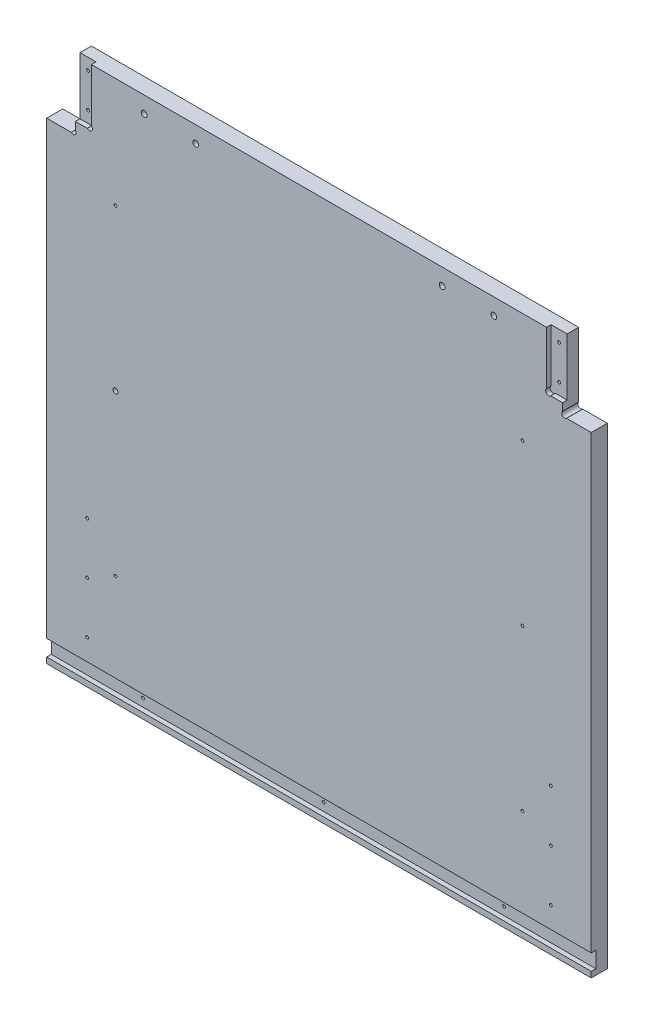
SolidWorks part; units mm, degrees
material "Pine"
ref_plane "Front Plane" through (0, 0, 0) normal (0, 0, 1) x (1, 0, 0)
ref_plane "Top Plane" through (0, 0, 0) normal (0, 1, 0) x (1, 0, 0)
ref_plane "Right Plane" through (0, 0, 0) normal (1, 0, 0) x (0, 0, -1)
sketch "Sketch1" plane through (0, 0, 0) normal (0, 0, 1) x (1, 0, 0)
  line L0 (8932.6508, -5243.5125) -> (10226.1458, -5243.5125)
  line L1 (9086.3208, -4722.0918) -> (10222.9708, -4853.7812)
  line L2 (8914.8708, -6342.0625) -> (10197.5708, -6342.0625)
  line L3 (8914.8708, -5808.6625) -> (10197.5708, -5808.6625)
  line L4 (8919.6333, -5253.0375) -> (10218.2083, -5253.0375)
  line L5 (9134.2633, -4656.1375) -> (9134.2633, -4638.3575)
  line L6 (9091.0833, -4638.3575) -> (9134.2633, -4638.3575)
  line L7 (9091.0833, -4567.2375) -> (9091.0833, -4638.3575)
  line L8 (9134.2633, -4656.1375) -> (9581.3033, -4656.1375)
  line L9 (9091.0833, -4567.2375) -> (9624.4833, -4567.2375)
  line L10 (9581.3033, -4656.1375) -> (9581.3033, -4638.3575)
  line L11 (9581.3033, -4638.3575) -> (9624.4833, -4638.3575)
  line L12 (9624.4833, -4567.2375) -> (9624.4833, -4638.3575)
  line L13 (8932.6508, -5225.7325) -> (9344.9775, -5225.7325)
  line L14 (8932.6508, -5256.2125) -> (8932.6508, -5243.5125)
  line L15 (8911.6958, -5256.2125) -> (8932.6508, -5256.2125)
  line L16 (8914.8708, -4722.0918) -> (9086.3208, -4722.0918)
  line L17 (8911.6958, -4715.5913) -> (8932.6508, -4715.5913)
  line L18 (8914.8708, -6342.0625) -> (8914.8708, -5808.6625)
  line L19 (12082.9917, -4722.0918) -> (10946.3417, -4853.7812)
  line L20 (12236.6617, -5243.5125) -> (10943.1667, -5243.5125)
  line L21 (10951.1042, -5253.0375) -> (12249.6792, -5253.0375)
  line L22 (10838.3917, -5656.2625) -> (11308.2917, -5656.2625)
  line L23 (10838.3917, -5719.7625) -> (11308.2917, -5719.7625)
  line L24 (10838.3917, -5742.5368) -> (11308.2917, -5742.5368)
  line L25 (10806.6417, -6342.0625) -> (11340.0417, -6342.0625)
  line L26 (10803.4667, -6335.7125) -> (11343.2167, -6335.7125)
  line L27 (10803.4667, -6317.9325) -> (11343.2167, -6317.9325)
  line L28 (10943.1667, -5225.7325) -> (11376.4483, -5225.7325)
  line L29 (11506.7292, -4754.5625) -> (10806.6417, -4827.5875)
  line L30 (11506.7292, -4567.2375) -> (11506.7292, -4754.5625)
  line L31 (10806.6417, -4567.2375) -> (10806.6417, -4827.5875)
  line L32 (10806.6417, -4567.2375) -> (11506.7292, -4567.2375)
  line L33 (10235.6708, -6329.3625) -> (10245.1958, -6329.3625)
  line L34 (10245.1958, -6329.3625) -> (10254.7208, -6278.5625)
  line L35 (10302.3458, -6329.3625) -> (10311.8708, -6278.5625)
  line L36 (10302.3458, -6329.3625) -> (10292.8208, -6329.3625)
  line L37 (10245.1958, -5821.3625) -> (10254.7208, -5872.1625)
  line L38 (10235.6708, -5821.3625) -> (10245.1958, -5821.3625)
  line L39 (10292.8208, -5821.3625) -> (10302.3458, -5821.3625)
  line L40 (10302.3458, -5821.3625) -> (10311.8708, -5872.1625)
  line L41 (10235.6708, -5821.3625) -> (10235.6708, -6329.3625)
  line L42 (10254.7208, -5872.1625) -> (10254.7208, -6278.5625)
  line L43 (10311.8708, -5872.1625) -> (10311.8708, -6278.5625)
  line L44 (10292.8208, -5821.3625) -> (10292.8208, -6329.3625)
  line L45 (8932.6508, -5225.7325) -> (8932.6508, -4715.5913)
  line L46 (8911.6958, -4715.5913) -> (8911.6958, -5256.2125)
  line L47 (8914.8708, -5248.275) -> (8914.8708, -4722.0918)
  line L48 (8919.6333, -5253.0375) -> (8914.8708, -5248.275)
  line L49 (8914.8708, -5145.0875) -> (8937.426, -5145.0875)
  line L50 (8914.8708, -5202.2375) -> (8937.426, -5202.2375)
  line L51 (10838.3917, -5656.2625) -> (10838.3917, -5719.7625)
  line L52 (10832.0417, -5736.1868) -> (10856.1717, -5736.1868)
  line L53 (10806.6417, -6342.0625) -> (10806.6417, -5818.7368)
  line L54 (10832.0417, -5649.9125) -> (10856.1717, -5649.9125)
  line L55 (10832.0417, -5726.1125) -> (10856.1717, -5726.1125)
  line L56 (10806.6417, -5818.7368) -> (10833.9015, -5818.7368)
  line L57 (10832.0417, -5806.0442) -> (10851.6815, -5806.0442)
  line L58 (10856.1717, -5801.5541) -> (10856.1717, -5736.1868)
  line L59 (10838.3917, -5814.2467) -> (10838.3917, -5742.5368)
  line L60 (10832.0417, -5806.0442) -> (10832.0417, -5736.1868)
  line L61 (10803.4667, -6317.9325) -> (10803.4667, -6335.7125)
  line L62 (10197.5708, -5808.6625) -> (10197.5708, -6342.0625)
  line L63 (9762.3842, -6348.4125) -> (9762.3842, -5802.3125)
  line L64 (9780.1642, -6348.4125) -> (9762.3842, -6348.4125)
  line L65 (9780.1642, -5802.3125) -> (9780.1642, -6348.4125)
  line L66 (9762.3842, -5802.3125) -> (9780.1642, -5802.3125)
  line L67 (9332.2775, -6348.4125) -> (9332.2775, -5802.3125)
  line L68 (9332.2775, -6348.4125) -> (9350.0575, -6348.4125)
  line L69 (9350.0575, -5802.3125) -> (9350.0575, -6348.4125)
  line L70 (9332.2775, -5802.3125) -> (9350.0575, -5802.3125)
  line L71 (9993.8374, -6061.075) -> (9993.8374, -6045.2418)
  line L72 (9998.5999, -6065.8375) -> (10014.4331, -6065.8375)
  line L73 (9998.5999, -6084.8875) -> (10014.4331, -6084.8875)
  line L74 (9993.8374, -6105.4832) -> (9993.8374, -6089.65)
  line L75 (9974.7874, -6105.4832) -> (9974.7874, -6089.65)
  line L76 (9954.1917, -6084.8875) -> (9970.0249, -6084.8875)
  line L77 (9974.7874, -6061.075) -> (9974.7874, -6045.2418)
  line L78 (9954.1917, -6065.8375) -> (9970.0249, -6065.8375)
  line L79 (10793.9417, -6237.2875) -> (10816.4969, -6237.2875)
  line L80 (10793.9417, -6294.4375) -> (10816.4969, -6294.4375)
  line L81 (10856.1717, -5649.9125) -> (10856.1717, -5726.1125)
  line L82 (10832.0417, -5726.1125) -> (10832.0417, -5649.9125)
  line L83 (10226.1458, -5225.7325) -> (10226.1458, -5243.5125)
  line L84 (10205.1908, -5257.8) -> (10205.1908, -4844.2499)
  line L85 (10230.9083, -4844.2499) -> (10230.9083, -5257.8)
  line L86 (10205.1908, -5257.8) -> (10230.9083, -5257.8)
  line L87 (10205.1908, -4844.2499) -> (10230.9083, -4844.2499)
  line L88 (10946.3417, -5176.8375) -> (10968.8969, -5176.8375)
  line L89 (9349.4676, -5141.9125) -> (9358.2674, -5141.9125)
  line L90 (10946.3417, -5119.6875) -> (10968.8969, -5119.6875)
  line L91 (9929.011, -4660.9635) -> (10066.0807, -4660.9635)
  line L92 (9929.011, -4678.7435) -> (10066.0807, -4678.7435)
  line L93 (10943.1667, -5225.7325) -> (10943.1667, -5243.5125)
  line L94 (10946.3417, -5248.275) -> (10951.1042, -5253.0375)
  line L95 (10946.3417, -5257.8063) -> (10946.3417, -4849.0188)
  line L96 (10964.1217, -5257.8) -> (10964.1217, -4844.2499)
  line L97 (10938.4042, -4844.2499) -> (10938.4042, -5257.8)
  line L98 (10938.4042, -5257.8) -> (10964.1217, -5257.8)
  line L99 (10964.1217, -4844.2499) -> (10938.4042, -4844.2499)
  line L100 (10344.8908, -4560.8875) -> (10369.0208, -4560.8875)
  line L101 (10344.8908, -4560.8875) -> (10369.0208, -4560.8875)
  line L102 (10800.2917, -4560.8875) -> (10824.4217, -4560.8875)
  line L103 (10200.4156, -5119.6875) -> (10222.9708, -5119.6875)
  line L104 (10200.4156, -5176.8375) -> (10222.9708, -5176.8375)
  line L105 (9344.9775, -5146.4026) -> (9344.9775, -5225.7325)
  line L106 (10344.8908, -4560.8875) -> (10344.8908, -4833.9375)
  line L107 (9792.8642, -5225.7325) -> (9792.8642, -5146.4026)
  line L108 (9362.7575, -5225.7325) -> (9775.0842, -5225.7325)
  line L109 (9680.3633, -4761.8396) -> (9680.3633, -4559.9604)
  line L110 (9656.2333, -4559.9604) -> (9680.3633, -4559.9604)
  line L111 (9656.2333, -4761.8396) -> (9680.3633, -4761.8396)
  line L112 (9656.2333, -4761.8396) -> (9656.2333, -4559.9604)
  line L113 (9779.5743, -5141.9125) -> (9788.374, -5141.9125)
  line L114 (10070.5708, -4665.4536) -> (10070.5708, -4674.2534)
  line L115 (9924.5208, -4674.2534) -> (9924.5208, -4665.4536)
  line L116 (12127.4417, -6188.3925) -> (12205.5015, -6188.3925)
  line L117 (12209.9917, -6170.6125) -> (12209.9917, -6183.9024)
  line L118 (9792.8642, -5225.7325) -> (10226.1458, -5225.7325)
  line L119 (9662.5833, -4754.5625) -> (10362.6708, -4827.5875)
  line L120 (9662.5833, -4567.2375) -> (9662.5833, -4754.5625)
  line L121 (10362.6708, -4567.2375) -> (10362.6708, -4827.5875)
  line L122 (9662.5833, -4567.2375) -> (10362.6708, -4567.2375)
  line L123 (10824.4217, -4833.9375) -> (10800.2917, -4833.9375)
  line L124 (10800.2917, -4833.9375) -> (10800.2917, -4560.8875)
  line L125 (10824.4217, -4560.8875) -> (10824.4217, -4833.9375)
  line L126 (10344.8908, -4833.9375) -> (10369.0208, -4833.9375)
  line L127 (10369.0208, -4833.9375) -> (10369.0208, -4560.8875)
  line L128 (10222.9708, -5248.275) -> (10218.2083, -5253.0375)
  line L129 (10222.9708, -5257.8063) -> (10222.9708, -4849.0188)
  line L130 (11734.6544, -5701.375) -> (11739.2301, -5701.375)
  line L131 (9362.7575, -5225.7325) -> (9362.7575, -5146.4026)
  line L132 (9775.0842, -5146.4026) -> (9775.0842, -5225.7325)
  line L133 (11761.3864, -5701.375) -> (11756.8282, -5701.375)
  line L134 (11734.6544, -5693.755) -> (11739.2301, -5693.755)
  line L135 (11761.4039, -5693.755) -> (11756.8282, -5693.755)
  line L136 (11734.6544, -5701.375) -> (11739.2301, -5701.375)
  line L137 (11744.3462, -5721.3024) -> (11744.3462, -5706.4179)
  line L138 (11751.7122, -5721.3024) -> (11751.7122, -5706.4179)
  line L139 (11740.0917, -6170.6125) -> (11740.0917, -6183.9024)
  line L140 (11689.2917, -6188.3925) -> (11822.6417, -6188.3925)
  line L141 (11689.2917, -6348.4093) -> (11689.2917, -6164.2657)
  line L142 (11689.2917, -6164.2657) -> (11746.4417, -6164.2657)
  line L143 (11746.4417, -6164.2657) -> (11746.4417, -6188.3925)
  line L144 (11689.2917, -6164.2657) -> (11746.4417, -6164.2657)
  line L145 (11340.0417, -5818.7368) -> (11340.0417, -6342.0625)
  line L146 (11290.5117, -5726.1125) -> (11314.6417, -5726.1125)
  line L147 (11290.5117, -5649.9125) -> (11290.5117, -5726.1125)
  line L148 (11340.0417, -5818.7368) -> (11312.7818, -5818.7368)
  line L149 (11314.6417, -5806.0442) -> (11295.0018, -5806.0442)
  line L150 (11290.5117, -5801.5541) -> (11290.5117, -5736.1868)
  line L151 (11308.2917, -5814.2467) -> (11308.2917, -5742.5368)
  line L152 (11314.6417, -5806.0442) -> (11314.6417, -5736.1868)
  line L153 (11290.5117, -5736.1868) -> (11314.6417, -5736.1868)
  line L154 (11848.0417, -6267.1325) -> (11962.3417, -6267.1325)
  line L155 (11962.3417, -6267.1325) -> (11962.3417, -6203.6325)
  line L156 (11343.2167, -6317.9325) -> (11343.2167, -6335.7125)
  line L157 (11365.4417, -5656.2625) -> (11365.4417, -5719.7625)
  line L158 (11365.4417, -5656.2625) -> (11479.7417, -5656.2625)
  line L159 (11778.1917, -6071.3937) -> (11802.3217, -6071.3937)
  line L160 (11314.6417, -5726.1125) -> (11314.6417, -5649.9125)
  line L161 (11314.6417, -5649.9125) -> (11290.5117, -5649.9125)
  line L162 (11308.2917, -5719.7625) -> (11308.2917, -5656.2625)
  line L163 (11689.2917, -6348.4093) -> (11713.4217, -6348.4093)
  line L164 (12203.6417, -6164.2657) -> (12260.7917, -6164.2657)
  line L165 (11713.4217, -6348.4093) -> (11713.4217, -6164.2657)
  line L166 (11695.6417, -6342.0625) -> (11695.6417, -6170.6125)
  line L167 (11695.6417, -6048.5337) -> (11699.4517, -6052.3437)
  line L168 (11822.6417, -6292.5325) -> (11822.6417, -6188.3925)
  line L169 (11695.6417, -6342.0625) -> (11695.6417, -6170.6125)
  line L170 (11848.0417, -6203.6325) -> (11962.3417, -6203.6325)
  line L171 (11848.0417, -6203.6325) -> (11848.0417, -6267.1325)
  line L172 (11987.7417, -6267.1325) -> (11987.7417, -6203.6325)
  line L173 (11784.5417, -6077.7437) -> (11784.5417, -6141.2438)
  line L174 (11517.8417, -5656.2625) -> (11632.1417, -5656.2625)
  line L175 (11632.1417, -5656.2625) -> (11632.1417, -5719.7625)
  line L176 (11632.1417, -5719.7625) -> (11517.8417, -5719.7625)
  line L177 (11517.8417, -5719.7625) -> (11517.8417, -5656.2625)
  line L178 (11692.4667, -6028.2137) -> (11692.4667, -6045.9937)
  line L179 (11695.6417, -5979.3188) -> (11718.1969, -5979.3188)
  line L180 (11695.6417, -5922.1687) -> (11718.1969, -5922.1687)
  line L181 (11821.0415, -5722.9375) -> (11821.0415, -5943.6)
  line L182 (11687.7042, -5651.5) -> (11701.9917, -5651.5)
  line L183 (11687.7042, -5651.5) -> (11687.7042, -6055.5251)
  line L184 (11687.7042, -6055.5251) -> (11701.9917, -6055.5251)
  line L185 (11701.9917, -6055.5251) -> (11701.9917, -5651.5)
  line L186 (11695.6417, -6055.2013) -> (11695.6417, -5649.595)
  line L187 (11695.6417, -5656.2625) -> (11695.6417, -6048.5337)
  line L188 (11695.6417, -6170.6125) -> (11740.0917, -6170.6125)
  line L189 (12203.6417, -6164.2657) -> (12203.6417, -6188.3925)
  line L190 (12254.4417, -6342.0625) -> (12254.4417, -6170.6125)
  line L191 (12129.0419, -5943.6) -> (12129.0419, -5722.9375)
  line L192 (12254.4417, -6048.5337) -> (12250.6317, -6052.3437)
  line L193 (12257.6167, -6045.9937) -> (12257.6167, -6028.2137)
  line L194 (12248.0917, -5651.5) -> (12262.3792, -5651.5)
  line L195 (12262.3792, -5651.5) -> (12262.3792, -6055.5251)
  line L196 (12262.3792, -6055.5251) -> (12248.0917, -6055.5251)
  line L197 (12248.0917, -6055.5251) -> (12248.0917, -5651.5)
  line L198 (12254.4417, -6141.2438) -> (12254.4417, -6077.7437)
  line L199 (12236.6617, -6164.2657) -> (12260.7917, -6164.2657)
  line L200 (12102.0417, -6267.1325) -> (11987.7417, -6267.1325)
  line L201 (11330.1865, -6237.2875) -> (11352.7417, -6237.2875)
  line L202 (11330.1865, -6294.4375) -> (11352.7417, -6294.4375)
  line L203 (11474.6617, -5851.8425) -> (11492.4417, -5851.8425)
  line L204 (11474.6617, -5808.6625) -> (11474.6617, -5851.8425)
  line L205 (11403.5417, -5808.6625) -> (11474.6617, -5808.6625)
  line L206 (11492.4417, -5851.8425) -> (11492.4417, -6298.8825)
  line L207 (11403.5417, -6342.0625) -> (11403.5417, -5808.6625)
  line L208 (11474.6617, -6298.8825) -> (11492.4417, -6298.8825)
  line L209 (11474.6617, -6342.0625) -> (11474.6617, -6298.8825)
  line L210 (11403.5417, -6342.0625) -> (11474.6617, -6342.0625)
  line L211 (11619.4417, -5851.8425) -> (11601.6617, -5851.8425)
  line L212 (11601.6617, -5808.6625) -> (11601.6617, -5851.8425)
  line L213 (11530.5417, -5808.6625) -> (11601.6617, -5808.6625)
  line L214 (11619.4417, -5851.8425) -> (11619.4417, -6298.8825)
  line L215 (11530.5417, -6342.0625) -> (11530.5417, -5808.6625)
  line L216 (11619.4417, -6298.8825) -> (11601.6617, -6298.8825)
  line L217 (11601.6617, -6342.0625) -> (11601.6617, -6298.8825)
  line L218 (11530.5417, -6342.0625) -> (11601.6617, -6342.0625)
  line L219 (11479.7417, -5719.7625) -> (11479.7417, -5656.2625)
  line L220 (11365.4417, -5719.7625) -> (11479.7417, -5719.7625)
  line L221 (11778.1917, -6147.5937) -> (11802.3217, -6147.5937)
  line L222 (11802.3217, -6071.3937) -> (11802.3217, -6147.5937)
  line L223 (11778.1917, -6147.5937) -> (11778.1917, -6071.3937)
  line L224 (12254.4417, -5922.1687) -> (12231.8865, -5922.1687)
  line L225 (12254.4417, -5979.3188) -> (12231.8865, -5979.3188)
  line L226 (12254.4417, -6055.2013) -> (12254.4417, -5649.595)
  line L227 (12254.4417, -6048.5337) -> (12254.4417, -5656.2625)
  line L228 (11841.6917, -5702.2873) -> (12108.3917, -5702.2873)
  line L229 (11822.6417, -6292.5325) -> (12127.4417, -6292.5325)
  line L230 (12127.4417, -6292.5325) -> (12127.4417, -6188.3925)
  line L231 (12254.4417, -6170.6125) -> (12209.9917, -6170.6125)
  line L232 (11695.6417, -6342.0625) -> (12254.4417, -6342.0625)
  line L233 (12236.6617, -6348.4093) -> (12260.7917, -6348.4093)
  line L234 (12260.7917, -6348.4093) -> (12260.7917, -6164.2657)
  line L235 (12236.6617, -6348.4093) -> (12236.6617, -6164.2657)
  line L236 (12102.0417, -6203.6325) -> (12102.0417, -6267.1325)
  line L237 (11987.7417, -6203.6325) -> (12102.0417, -6203.6325)
  line L238 (12236.6617, -6147.5937) -> (12236.6617, -6071.3937)
  line L239 (12203.6417, -6188.3925) -> (12260.7917, -6188.3925)
  line L240 (11098.7417, -4665.4536) -> (11098.7417, -4674.2534)
  line L241 (11394.2283, -5146.4026) -> (11394.2283, -5225.7325)
  line L242 (11376.4483, -5225.7325) -> (11376.4483, -5146.4026)
  line L243 (11394.2283, -5225.7325) -> (11806.555, -5225.7325)
  line L244 (11841.6917, -5964.2502) -> (12108.3917, -5964.2502)
  line L245 (12236.6617, -6147.5937) -> (12260.7917, -6147.5937)
  line L246 (12236.6617, -5256.2125) -> (12236.6617, -5243.5125)
  line L247 (12260.7917, -6147.5937) -> (12260.7917, -6071.3937)
  line L248 (12260.7917, -6071.3937) -> (12236.6617, -6071.3937)
  line L249 (12254.4417, -6077.7437) -> (11784.5417, -6077.7437)
  line L250 (11784.5417, -6141.2438) -> (12254.4417, -6141.2438)
  line L252 (12254.4417, -5656.2625) -> (11695.6417, -5656.2625)
  line L253 (11699.4517, -6052.3437) -> (12250.6317, -6052.3437)
  line L254 (11692.4667, -6045.9937) -> (12257.6167, -6045.9937)
  line L255 (11692.4667, -6028.2137) -> (12257.6167, -6028.2137)
  line L256 (11824.335, -5146.4026) -> (11824.335, -5225.7325)
  line L257 (11811.0451, -5141.9125) -> (11819.8449, -5141.9125)
  line L258 (11244.7917, -4674.2534) -> (11244.7917, -4665.4536)
  line L259 (11806.555, -5225.7325) -> (11806.555, -5146.4026)
  line L260 (11488.9492, -4761.8396) -> (11488.9492, -4559.9604)
  line L261 (11488.9492, -4559.9604) -> (11513.0792, -4559.9604)
  line L262 (11488.9492, -4761.8396) -> (11513.0792, -4761.8396)
  line L263 (11513.0792, -4761.8396) -> (11513.0792, -4559.9604)
  line L264 (11240.3015, -4660.9635) -> (11103.2318, -4660.9635)
  line L265 (11103.2318, -4678.7435) -> (11240.3015, -4678.7435)
  line L266 (12236.6617, -5225.7325) -> (12236.6617, -4715.5913)
  line L267 (12257.6167, -4715.5913) -> (12257.6167, -5256.2125)
  line L268 (12254.4417, -5248.275) -> (12254.4417, -4722.0918)
  line L269 (12236.6617, -5225.7325) -> (11824.335, -5225.7325)
  line L270 (12035.0492, -4656.1375) -> (12035.0492, -4638.3575)
  line L271 (12078.2292, -4638.3575) -> (12035.0492, -4638.3575)
  line L272 (12078.2292, -4567.2375) -> (12078.2292, -4638.3575)
  line L273 (12035.0492, -4656.1375) -> (11588.0092, -4656.1375)
  line L274 (11544.8292, -4567.2375) -> (12078.2292, -4567.2375)
  line L275 (11588.0092, -4656.1375) -> (11588.0092, -4638.3575)
  line L276 (11544.8292, -4638.3575) -> (11588.0092, -4638.3575)
  line L277 (11544.8292, -4567.2375) -> (11544.8292, -4638.3575)
  line L278 (12249.6792, -5253.0375) -> (12254.4417, -5248.275)
  line L280 (12257.6167, -5256.2125) -> (12236.6617, -5256.2125)
  line L281 (12231.8865, -5145.0875) -> (12254.4417, -5145.0875)
  line L282 (12231.8865, -5202.2375) -> (12254.4417, -5202.2375)
  line L283 (12236.6617, -4715.5913) -> (12257.6167, -4715.5913)
  line L284 (12082.9917, -4722.0918) -> (12254.4417, -4722.0918)
  line L285 (11380.9385, -5141.9125) -> (11389.7382, -5141.9125)
  circle A0 centre (8923.7608, -4778.9042) radius 1.5875
  circle A1 centre (9062.6598, -4736.3765) radius 2.3685
  circle A2 centre (9051.3958, -6281.7375) radius 22.225
  circle A3 centre (9083.1458, -6249.9875) radius 1.5875
  circle A4 centre (9083.1458, -6313.4875) radius 1.5875
  circle A5 centre (9019.6458, -6249.9875) radius 1.5875
  circle A6 centre (9019.6458, -6313.4875) radius 1.5875
  circle A7 centre (8972.3383, -5202.2375) radius 1.5875
  circle A8 centre (8923.7608, -5015.9708) radius 1.5875
  circle A9 centre (8923.7608, -5134.5042) radius 1.5875
  circle A10 centre (9054.5708, -5234.6225) radius 1.5875
  circle A11 centre (8923.7608, -4897.4375) radius 1.5875
  circle A12 centre (8972.3383, -5087.9375) radius 1.5875
  circle A13 centre (8972.3383, -5145.0875) radius 1.5875
  circle A14 centre (10847.2817, -5668.9625) radius 1.5875
  circle A15 centre (10847.2817, -5707.0625) radius 1.5875
  circle A16 centre (10847.2817, -5755.2368) radius 1.5875
  circle A17 centre (10851.4092, -6237.2875) radius 1.5875
  circle A18 centre (10851.4092, -6294.4375) radius 1.5875
  circle A19 centre (10847.2817, -5793.3442) radius 1.5875
  arc A20 (10833.9015, -5818.7368) -> (10838.3917, -5814.2467) centre (10836.1466, -5816.4918) ccw
  arc A21 (10851.6815, -5806.0442) -> (10856.1717, -5801.5541) centre (10853.9266, -5803.7992) ccw
  circle A22 centre (10882.8417, -6040.4375) radius 1.5875
  circle A23 centre (10882.8417, -6218.2375) radius 1.5875
  circle A24 centre (10882.8417, -5862.6375) radius 1.5875
  circle A25 centre (10908.2417, -6326.8225) radius 1.5875
  circle A26 centre (10908.2417, -6326.8225) radius 1.5875
  circle A27 centre (10851.4092, -6180.1375) radius 1.5875
  circle A28 centre (10815.5317, -4783.4231) radius 1.5875
  circle A29 centre (10815.5317, -4696.9488) radius 1.5875
  circle A30 centre (10815.5317, -4610.4746) radius 1.5875
  circle A31 centre (10979.1323, -4867.0082) radius 2.3685
  circle A32 centre (10190.1802, -4867.0082) radius 2.3685
  circle A33 centre (10955.2317, -4929.9812) radius 1.5875
  circle A34 centre (10955.2317, -5031.5812) radius 1.5875
  circle A35 centre (10214.0808, -4929.9812) radius 1.5875
  circle A36 centre (10214.0808, -5031.5812) radius 1.5875
  circle A37 centre (9341.1675, -6265.8625) radius 1.5875
  circle A38 centre (9771.2742, -5884.8625) radius 1.5875
  circle A39 centre (9771.2742, -6138.8625) radius 1.5875
  circle A40 centre (9771.2742, -6011.8625) radius 1.5875
  arc A41 (10036.2287, -6113.8083) -> (10051.3426, -6111.6033) centre (10042.9639, -6107.0732) ccw
  arc A42 (10051.3426, -6111.6033) -> (10051.3426, -6039.1217) centre (9984.3124, -6075.3625) ccw
  arc A43 (10051.3426, -6039.1217) -> (10036.2287, -6036.9167) centre (10042.9639, -6043.6518) ccw
  arc A44 (10034.5851, -6102.5431) -> (10034.5851, -6048.1819) centre (9984.3124, -6075.3625) ccw
  arc A45 (10034.5851, -6102.5431) -> (10036.2287, -6113.8083) centre (10042.9639, -6107.0732) ccw
  arc A46 (10036.2287, -6036.9167) -> (10034.5851, -6048.1819) centre (10042.9639, -6043.6518) ccw
  arc A47 (9945.8666, -6127.2787) -> (9948.0717, -6142.3927) centre (9952.6018, -6134.0139) ccw
  arc A48 (9948.0717, -6142.3927) -> (10020.5532, -6142.3927) centre (9984.3124, -6075.3625) ccw
  arc A49 (10020.5532, -6142.3927) -> (10022.7583, -6127.2787) centre (10016.0231, -6134.0139) ccw
  arc A50 (9957.1319, -6125.6352) -> (10011.493, -6125.6352) centre (9984.3124, -6075.3625) ccw
  arc A51 (9957.1319, -6125.6352) -> (9945.8666, -6127.2787) centre (9952.6018, -6134.0139) ccw
  arc A52 (10022.7583, -6127.2787) -> (10011.493, -6125.6352) centre (10016.0231, -6134.0139) ccw
  arc A53 (9932.3962, -6036.9167) -> (9917.2822, -6039.1217) centre (9925.661, -6043.6518) ccw
  arc A54 (9917.2822, -6039.1217) -> (9917.2822, -6111.6033) centre (9984.3124, -6075.3625) ccw
  arc A55 (9917.2822, -6111.6033) -> (9932.3962, -6113.8083) centre (9925.661, -6107.0732) ccw
  arc A56 (9934.0398, -6048.1819) -> (9934.0398, -6102.5431) centre (9984.3124, -6075.3625) ccw
  arc A57 (9934.0398, -6048.1819) -> (9932.3962, -6036.9167) centre (9925.661, -6043.6518) ccw
  arc A58 (9932.3962, -6113.8083) -> (9934.0398, -6102.5431) centre (9925.661, -6107.0732) ccw
  arc A59 (9945.8666, -6023.4463) -> (9957.1319, -6025.0898) centre (9952.6018, -6016.7111) ccw
  arc A60 (10011.493, -6025.0898) -> (10022.7583, -6023.4463) centre (10016.0231, -6016.7111) ccw
  arc A61 (10011.493, -6025.0898) -> (9957.1319, -6025.0898) centre (9984.3124, -6075.3625) ccw
  arc A62 (9948.0717, -6008.3323) -> (9945.8666, -6023.4463) centre (9952.6018, -6016.7111) ccw
  arc A63 (10020.5532, -6008.3323) -> (9948.0717, -6008.3323) centre (9984.3124, -6075.3625) ccw
  arc A64 (10022.7583, -6023.4463) -> (10020.5532, -6008.3323) centre (10016.0231, -6016.7111) ccw
  arc A65 (10005.0943, -6187.7574) -> (10096.7073, -6096.1443) centre (9984.3124, -6075.3625) ccw
  arc A66 (9993.8374, -6178.3911) -> (10005.0943, -6187.7574) centre (10003.3624, -6178.3911) ccw
  arc A67 (10001.6306, -6169.0249) -> (10077.9748, -6092.6807) centre (9984.3124, -6075.3625) ccw
  arc A68 (10087.3411, -6084.8875) -> (10077.9748, -6092.6807) centre (10087.3411, -6094.4125) ccw
  arc A69 (10001.6306, -6169.0249) -> (9993.8374, -6178.3911) centre (10003.3624, -6178.3911) ccw
  arc A70 (9963.5306, -6187.7574) -> (9974.7874, -6178.3911) centre (9965.2624, -6178.3911) ccw
  arc A71 (9871.9176, -6096.1443) -> (9963.5306, -6187.7574) centre (9984.3124, -6075.3625) ccw
  arc A72 (9881.2838, -6084.8875) -> (9871.9176, -6096.1443) centre (9881.2838, -6094.4125) ccw
  arc A73 (9890.65, -6092.6807) -> (9966.9943, -6169.0249) centre (9984.3124, -6075.3625) ccw
  arc A74 (9974.7874, -6178.3911) -> (9966.9943, -6169.0249) centre (9965.2624, -6178.3911) ccw
  arc A75 (9890.65, -6092.6807) -> (9881.2838, -6084.8875) centre (9881.2838, -6094.4125) ccw
  arc A76 (9871.9176, -6054.5807) -> (9881.2838, -6065.8375) centre (9881.2838, -6056.3125) ccw
  arc A77 (9963.5306, -5962.9676) -> (9871.9176, -6054.5807) centre (9984.3124, -6075.3625) ccw
  arc A78 (9974.7874, -5972.3339) -> (9963.5306, -5962.9676) centre (9965.2624, -5972.3339) ccw
  arc A79 (9966.9943, -5981.7001) -> (9890.65, -6058.0443) centre (9984.3124, -6075.3625) ccw
  arc A80 (9881.2838, -6065.8375) -> (9890.65, -6058.0443) centre (9881.2838, -6056.3125) ccw
  arc A81 (9966.9943, -5981.7001) -> (9974.7874, -5972.3339) centre (9965.2624, -5972.3339) ccw
  arc A82 (10077.9748, -6058.0443) -> (10087.3411, -6065.8375) centre (10087.3411, -6056.3125) ccw
  arc A83 (9993.8374, -5972.3339) -> (10001.6306, -5981.7001) centre (10003.3624, -5972.3339) ccw
  arc A84 (10077.9748, -6058.0443) -> (10001.6306, -5981.7001) centre (9984.3124, -6075.3625) ccw
  arc A85 (10087.3411, -6065.8375) -> (10096.7073, -6054.5807) centre (10087.3411, -6056.3125) ccw
  arc A86 (10096.7073, -6054.5807) -> (10005.0943, -5962.9676) centre (9984.3124, -6075.3625) ccw
  arc A87 (10005.0943, -5962.9676) -> (9993.8374, -5972.3339) centre (10003.3624, -5972.3339) ccw
  arc A88 (10014.4331, -6065.8375) -> (10018.7361, -6059.0339) centre (10014.4331, -6061.075) ccw
  arc A89 (10018.7361, -6059.0339) -> (10000.641, -6040.9388) centre (9984.3124, -6075.3625) ccw
  arc A90 (10000.641, -6040.9388) -> (9993.8374, -6045.2418) centre (9998.5999, -6045.2418) ccw
  arc A91 (9993.8374, -6061.075) -> (9998.5999, -6065.8375) centre (9998.5999, -6061.075) ccw
  arc A92 (9993.8374, -6105.4832) -> (10000.641, -6109.7862) centre (9998.5999, -6105.4832) ccw
  arc A93 (10000.641, -6109.7862) -> (10018.7361, -6091.6911) centre (9984.3124, -6075.3625) ccw
  arc A94 (10018.7361, -6091.6911) -> (10014.4331, -6084.8875) centre (10014.4331, -6089.65) ccw
  arc A95 (9998.5999, -6084.8875) -> (9993.8374, -6089.65) centre (9998.5999, -6089.65) ccw
  arc A96 (9954.1917, -6084.8875) -> (9949.8888, -6091.6911) centre (9954.1917, -6089.65) ccw
  arc A97 (9949.8888, -6091.6911) -> (9967.9839, -6109.7862) centre (9984.3124, -6075.3625) ccw
  arc A98 (9967.9839, -6109.7862) -> (9974.7874, -6105.4832) centre (9970.0249, -6105.4832) ccw
  arc A99 (9974.7874, -6089.65) -> (9970.0249, -6084.8875) centre (9970.0249, -6089.65) ccw
  arc A100 (9970.0249, -6065.8375) -> (9974.7874, -6061.075) centre (9970.0249, -6061.075) ccw
  arc A101 (9949.8888, -6059.0339) -> (9954.1917, -6065.8375) centre (9954.1917, -6061.075) ccw
  arc A102 (9967.9839, -6040.9388) -> (9949.8888, -6059.0339) centre (9984.3124, -6075.3625) ccw
  arc A103 (9974.7874, -6045.2418) -> (9967.9839, -6040.9388) centre (9970.0249, -6045.2418) ccw
  arc A104 (10096.7073, -6096.1443) -> (10087.3411, -6084.8875) centre (10087.3411, -6094.4125) ccw
  circle A105 centre (9771.2742, -6265.8625) radius 1.5875
  circle A106 centre (9341.1675, -5884.8625) radius 1.5875
  circle A107 centre (9341.1675, -6138.8625) radius 1.5875
  circle A108 centre (9341.1675, -6011.8625) radius 1.5875
  circle A109 centre (11037.2315, -4887.5494) radius 15.0812
  arc A110 (9349.4676, -5141.9125) -> (9344.9775, -5146.4026) centre (9347.2226, -5144.1576) ccw
  arc A111 (9362.7575, -5146.4026) -> (9358.2674, -5141.9125) centre (9360.5124, -5144.1576) ccw
  circle A112 centre (9946.7458, -4669.8535) radius 1.5875
  arc A113 (9924.5208, -4674.2534) -> (9929.011, -4678.7435) centre (9926.7659, -4676.4984) ccw
  circle A114 centre (11003.8092, -5176.8375) radius 1.5875
  circle A115 centre (11003.8092, -5119.6875) radius 1.5875
  circle A116 centre (10353.7808, -4696.9488) radius 1.5875
  circle A117 centre (10353.7808, -4610.4746) radius 1.5875
  circle A118 centre (10353.7808, -4783.4231) radius 1.5875
  circle A119 centre (11003.8092, -5062.5375) radius 1.5875
  circle A120 centre (9353.8675, -5160.9625) radius 1.5875
  circle A121 centre (9638.7708, -5234.6225) radius 1.5875
  circle A122 centre (9671.4733, -4724.1144) radius 1.5875
  circle A123 centre (9671.4733, -4661.3637) radius 1.5875
  circle A124 centre (9671.4733, -4598.6129) radius 1.5875
  arc A125 (9792.8642, -5146.4026) -> (9788.374, -5141.9125) centre (9790.6191, -5144.1576) ccw
  arc A126 (9779.5743, -5141.9125) -> (9775.0842, -5146.4026) centre (9777.3292, -5144.1576) ccw
  circle A127 centre (10048.3458, -4669.8535) radius 1.5875
  arc A128 (10070.5708, -4665.4536) -> (10066.0807, -4660.9635) centre (10068.3258, -4663.2086) ccw
  arc A129 (10066.0807, -4678.7435) -> (10070.5708, -4674.2534) centre (10068.3258, -4676.4984) ccw
  circle A130 centre (9997.5458, -4669.8535) radius 1.5875
  arc A131 (9929.011, -4660.9635) -> (9924.5208, -4665.4536) centre (9926.7659, -4663.2086) ccw
  circle A132 centre (10132.081, -4887.5494) radius 15.0812
  circle A133 centre (10165.5033, -5176.8375) radius 1.5875
  circle A134 centre (10165.5033, -5119.6875) radius 1.5875
  circle A135 centre (9486.3708, -5234.6225) radius 1.5875
  circle A136 centre (10165.5033, -5062.5375) radius 1.5875
  circle A137 centre (9206.9708, -5234.6225) radius 1.5875
  circle A138 centre (10070.5708, -5234.6225) radius 1.5875
  circle A139 centre (9918.1708, -5234.6225) radius 1.5875
  circle A140 centre (9783.9742, -5160.9625) radius 1.5875
  circle A141 centre (9783.9742, -5193.9825) radius 1.5875
  circle A142 centre (9353.8675, -5193.9825) radius 1.5875
  circle A143 centre (11073.3417, -6326.8225) radius 1.5875
  circle A144 centre (11073.3417, -6326.8225) radius 1.5875
  circle A145 centre (11295.2742, -6180.1375) radius 1.5875
  circle A146 centre (11295.2742, -6294.4375) radius 1.5875
  circle A147 centre (11295.2742, -6237.2875) radius 1.5875
  circle A148 centre (11975.0417, -5692.775) radius 3.4925
  circle A149 centre (11263.8417, -5862.6375) radius 1.5875
  arc A150 (11739.2301, -5701.375) -> (11744.3462, -5706.4179) centre (11748.0292, -5697.565) ccw
  arc A151 (11751.7122, -5706.4179) -> (11756.8282, -5701.375) centre (11748.0292, -5697.565) ccw
  arc A152 (11744.3462, -5721.3024) -> (11751.7122, -5721.3024) centre (11748.0292, -5725.505) ccw
  arc A153 (11734.6544, -5693.755) -> (11724.9787, -5697.565) centre (11730.5667, -5697.565) ccw
  arc A154 (11756.8282, -5693.755) -> (11739.2301, -5693.755) centre (11748.0292, -5697.565) ccw
  arc A155 (11724.9787, -5697.565) -> (11734.6544, -5701.375) centre (11730.5667, -5697.565) ccw
  arc A156 (11761.3864, -5701.375) -> (11771.0797, -5697.565) centre (11765.4842, -5697.565) ccw
  arc A157 (11771.0797, -5697.565) -> (11761.4039, -5693.755) centre (11765.4917, -5697.565) ccw
  arc A158 (11740.0917, -6183.9024) -> (11744.5818, -6188.3925) centre (11742.3367, -6186.1474) ccw
  arc A159 (12205.5015, -6188.3925) -> (12209.9917, -6183.9024) centre (12207.7466, -6186.1474) ccw
  circle A160 centre (11299.4017, -5793.3442) radius 1.5875
  arc A161 (11308.2917, -5814.2467) -> (11312.7818, -5818.7368) centre (11310.5367, -5816.4918) ccw
  arc A162 (11290.5117, -5801.5541) -> (11295.0018, -5806.0442) centre (11292.7567, -5803.7992) ccw
  circle A163 centre (11704.5317, -6314.149) radius 1.5875
  circle A164 centre (11748.9817, -6208.7125) radius 1.5875
  circle A165 centre (11263.8417, -6218.2375) radius 1.5875
  circle A166 centre (11263.8417, -6040.4375) radius 1.5875
  circle A167 centre (11238.4417, -6326.8225) radius 1.5875
  circle A168 centre (11238.4417, -6326.8225) radius 1.5875
  circle A169 centre (11299.4017, -5668.9625) radius 1.5875
  circle A170 centre (11299.4017, -5707.0625) radius 1.5875
  circle A171 centre (11726.7567, -6179.5025) radius 1.5875
  circle A172 centre (11704.5317, -6199.3198) radius 1.5875
  circle A173 centre (11748.9817, -6272.2125) radius 1.5875
  circle A174 centre (11704.5317, -6256.7344) radius 1.5875
  circle A175 centre (11299.4017, -5755.2368) radius 1.5875
  circle A176 centre (11913.4467, -6301.4225) radius 1.5875
  circle A177 centre (11790.2567, -6301.4225) radius 1.5875
  circle A178 centre (11793.4317, -6128.5437) radius 1.5875
  circle A179 centre (11753.1092, -5865.0188) radius 1.5875
  circle A180 centre (11809.9417, -6037.1038) radius 1.5875
  circle A181 centre (11809.9417, -6037.1038) radius 1.5875
  circle A182 centre (11753.1092, -5922.1687) radius 1.5875
  circle A183 centre (11975.0417, -5973.7625) radius 3.4925
  circle A184 centre (11975.0417, -6037.1038) radius 1.5875
  circle A185 centre (11753.1092, -5979.3188) radius 1.5875
  circle A186 centre (11975.0417, -6037.1038) radius 1.5875
  arc A187 (11841.6917, -5702.2873) -> (11821.0415, -5722.9375) centre (11841.6917, -5722.9375) ccw
  circle A188 centre (11811.5292, -5833.2687) radius 3.4925
  arc A189 (11821.0415, -5943.6) -> (11841.6917, -5964.2502) centre (11841.6917, -5943.6) ccw
  circle A190 centre (12196.9742, -5865.0188) radius 1.5875
  arc A191 (12129.0419, -5722.9375) -> (12108.3917, -5702.2873) centre (12108.3917, -5722.9375) ccw
  circle A192 centre (12036.6367, -6301.4225) radius 1.5875
  circle A193 centre (12159.8267, -6301.4225) radius 1.5875
  circle A194 centre (12138.5542, -5833.2687) radius 3.4925
  circle A195 centre (12197.2917, -5761.0375) radius 15.0812
  circle A196 centre (11793.4317, -6090.4437) radius 1.5875
  circle A197 centre (12196.9742, -5922.1687) radius 1.5875
  arc A198 (12108.3917, -5964.2502) -> (12129.0419, -5943.6) centre (12108.3917, -5943.6) ccw
  circle A199 centre (12196.9742, -5979.3188) radius 1.5875
  circle A200 centre (12201.1017, -6272.2125) radius 1.5875
  circle A201 centre (12245.5517, -6314.149) radius 1.5875
  circle A202 centre (12245.5517, -6256.7344) radius 1.5875
  circle A203 centre (12201.1017, -6208.7125) radius 1.5875
  circle A204 centre (12223.3267, -6179.5025) radius 1.5875
  circle A205 centre (12245.5517, -6199.3198) radius 1.5875
  circle A206 centre (11171.7667, -4669.8535) radius 1.5875
  circle A207 centre (11222.5667, -4669.8535) radius 1.5875
  arc A208 (11240.3015, -4678.7435) -> (11244.7917, -4674.2534) centre (11242.5466, -4676.4984) ccw
  circle A209 centre (11385.3383, -5193.9825) radius 1.5875
  circle A210 centre (12106.6527, -4736.3765) radius 2.3685
  circle A211 centre (12140.1417, -6037.1038) radius 1.5875
  circle A212 centre (12140.1417, -6037.1038) radius 1.5875
  circle A213 centre (12245.5517, -6090.4437) radius 1.5875
  circle A214 centre (12245.5517, -6128.5437) radius 1.5875
  circle A215 centre (11385.3383, -5160.9625) radius 1.5875
  arc A216 (11824.335, -5146.4026) -> (11819.8449, -5141.9125) centre (11822.0899, -5144.1576) ccw
  arc A217 (11811.0451, -5141.9125) -> (11806.555, -5146.4026) centre (11808.8001, -5144.1576) ccw
  circle A218 centre (11815.445, -5193.9825) radius 1.5875
  circle A219 centre (11815.445, -5160.9625) radius 1.5875
  circle A220 centre (11530.5417, -5234.6225) radius 1.5875
  circle A221 centre (11962.3417, -5234.6225) radius 1.5875
  arc A222 (11244.7917, -4665.4536) -> (11240.3015, -4660.9635) centre (11242.5466, -4663.2086) ccw
  circle A223 centre (11682.9417, -5234.6225) radius 1.5875
  circle A224 centre (11497.8392, -4724.1144) radius 1.5875
  circle A225 centre (11497.8392, -4661.3637) radius 1.5875
  circle A226 centre (11497.8392, -4598.6129) radius 1.5875
  circle A227 centre (11120.9667, -4669.8535) radius 1.5875
  arc A228 (11103.2318, -4660.9635) -> (11098.7417, -4665.4536) centre (11100.9867, -4663.2086) ccw
  arc A229 (11098.7417, -4674.2534) -> (11103.2318, -4678.7435) centre (11100.9867, -4676.4984) ccw
  circle A230 centre (12196.9742, -5202.2375) radius 1.5875
  circle A231 centre (12245.5517, -5015.9708) radius 1.5875
  circle A232 centre (12245.5517, -5134.5042) radius 1.5875
  circle A233 centre (12114.7417, -5234.6225) radius 1.5875
  circle A234 centre (12245.5517, -4897.4375) radius 1.5875
  circle A235 centre (12245.5517, -4778.9042) radius 1.5875
  circle A236 centre (12196.9742, -5087.9375) radius 1.5875
  circle A237 centre (12196.9742, -5145.0875) radius 1.5875
  circle A238 centre (11098.7417, -5234.6225) radius 1.5875
  circle A239 centre (11251.1417, -5234.6225) radius 1.5875
  arc A240 (11380.9385, -5141.9125) -> (11376.4483, -5146.4026) centre (11378.6934, -5144.1576) ccw
  arc A241 (11394.2283, -5146.4026) -> (11389.7382, -5141.9125) centre (11391.9833, -5144.1576) ccw
sketch "Sketch3" plane through (0, 0, 0) normal (0, 0, 1) x (1, 0, 0)
  line L0 (10806.6417, -6342.0625) -> (11409.8917, -6342.0625)
  line L1 (11409.8917, -6342.0625) -> (11409.8917, -5818.7368)
  line L2 (11409.8917, -5818.7368) -> (11378.1417, -5818.7368)
  line L4 (11378.1417, -5818.7368) -> (11378.1417, -5742.5368)
  line L5 (10838.3917, -5742.5368) -> (10838.3917, -5818.7368)
  line L7 (10838.3917, -5818.7368) -> (10806.6417, -5818.7368)
  line L8 (10806.6417, -5818.7368) -> (10806.6417, -6342.0625)
  line L9 (10838.3917, -5742.5368) -> (11378.1417, -5742.5368)
  dimension "D1" = 603.25
  dimension "D2" = 599.5257
  dimension "D3" = 31.75
  dimension "D4" = 76.2
extrude "Extrude1" add sketch "Sketch3" against normal blind 17.78
sketch "Sketch4" plane through (0, 0, 0) normal (0, 0, 1) x (1, 0, 0)
  line L0 (10838.3917, -5818.7368) -> (10836.1466, -5816.4918) construction
  line L1 (11378.1417, -5818.7368) -> (11380.3867, -5816.4918) construction
  line L2 (11409.8917, -5818.7368) -> (11378.1417, -5818.7368) construction
  line L3 (10838.3917, -5818.7368) -> (10806.6417, -5818.7368) construction
  circle A0 centre (11380.3867, -5816.4918) radius 3.175
  circle A1 centre (10836.1466, -5816.4918) radius 3.175
  dimension "D1" = 3.175
  dimension "D2" = 45
  dimension "D3" = 3.175
  dimension "D4" = 45
extrude "Cut-Extrude1" cut sketch "Sketch4" against normal up to surface (17.78 mm away) up to face at (11108.2667, -5930.5183, -17.78)
sketch "Sketch6" plane through (0, 0, 0) normal (0, 0, 1) x (1, 0, 0)
  line L0 (11108.2667, -6342.0625) -> (11108.2667, -6326.8225) construction
  line L1 (10806.6417, -6342.0625) -> (11409.8917, -6342.0625) construction
  line L2 (11108.2667, -6326.8225) -> (10908.2417, -6326.8225) construction
  line L3 (11108.2667, -6326.8225) -> (11308.2917, -6326.8225) construction
  line L4 (10847.2817, -5793.3442) -> (10847.2817, -5755.2368) construction
  line L5 (10847.2817, -5755.2368) -> (10847.2817, -5742.5368) construction
  line L6 (11378.1417, -5742.5368) -> (10838.3917, -5742.5368) construction
  line L7 (10847.2817, -5742.5368) -> (10838.3917, -5742.5368) construction
  line L8 (11369.2517, -5793.3442) -> (11369.2517, -5755.2368) construction
  line L9 (11369.2517, -5755.2368) -> (11369.2517, -5742.5368) construction
  line L10 (11369.2517, -5742.5368) -> (11378.1417, -5742.5368) construction
  line L11 (10806.6417, -6342.0625) -> (10806.6417, -5742.5368) construction
  line L12 (10806.6417, -6042.2997) -> (10882.8417, -6042.2997) construction
  line L13 (10882.8417, -5864.4997) -> (10882.8417, -6042.2997) construction
  line L14 (10806.6417, -5742.5368) -> (10838.3917, -5742.5368) construction
  line L15 (10882.8417, -6042.2997) -> (10882.8417, -6220.0997) construction
  line L16 (11409.8917, -6342.0625) -> (11409.8917, -5742.5368) construction
  line L17 (11409.8917, -5742.5368) -> (11378.1417, -5742.5368) construction
  line L18 (11409.8917, -6042.2997) -> (11333.6917, -6042.2997) construction
  line L19 (11333.6917, -5864.4997) -> (11333.6917, -6042.2997) construction
  line L20 (11333.6917, -6042.2997) -> (11333.6917, -6220.0997) construction
  line L21 (10851.4092, -6294.4375) -> (10851.4092, -6237.2875) construction
  line L22 (10851.4092, -6237.2875) -> (10851.4092, -6180.1375) construction
  line L23 (11365.1242, -6294.4375) -> (11365.1242, -6237.2875) construction
  line L24 (11365.1242, -6237.2875) -> (11365.1242, -6180.1375) construction
  circle A0 centre (10851.4092, -6294.4375) radius 1.5875
  circle A1 centre (10908.2417, -6326.8225) radius 1.5875
  circle A2 centre (11108.2667, -6326.8225) radius 1.5875
  circle A3 centre (11308.2917, -6326.8225) radius 1.5875
  circle A4 centre (11365.1242, -6294.4375) radius 1.5875
  circle A5 centre (11365.1242, -6237.2875) radius 1.5875
  circle A6 centre (11333.6917, -6220.0997) radius 1.5875
  circle A7 centre (11365.1242, -6180.1375) radius 1.5875
  circle A8 centre (11333.6917, -6042.2997) radius 1.5875
  circle A9 centre (11333.6917, -5864.4997) radius 1.5875
  circle A10 centre (11369.2517, -5793.3442) radius 1.5875
  circle A11 centre (11369.2517, -5755.2368) radius 1.5875
  circle A12 centre (10847.2817, -5755.2368) radius 1.5875
  circle A13 centre (10847.2817, -5793.3442) radius 1.5875
  circle A14 centre (10882.8417, -6042.2997) radius 2.7778
  circle A15 centre (10851.4092, -6180.1375) radius 1.5875
  circle A16 centre (10882.8417, -6220.0997) radius 1.5875
  circle A17 centre (10851.4092, -6237.2875) radius 1.5875
  circle A18 centre (10882.8417, -5864.4997) radius 1.5875
  dimension "D1" = 8.89
  dimension "D2" = 8.89
  dimension "D3" = 177.8
  dimension "D4" = 177.8
  dimension "D5" = 76.2
  dimension "D6" = 177.8
  dimension "D7" = 76.2
  dimension "D8" = 177.8
  dimension "D9" = 44.7675
  dimension "D10" = 104.775
  dimension "D11" = 44.7675
  dimension "D12" = 104.775
extrude "Cut-Extrude3" cut sketch "Sketch6" against normal up to surface (17.78 mm away) up to face at (11108.2667, -5907.713, -17.78)
sketch "Sketch5" plane through (0, 0, 0) normal (0, 0, 1) x (1, 0, 0)
  line L0 (11108.2667, -6317.9325) -> (11108.2667, -6342.0625) construction
  line L1 (10803.4667, -6317.9325) -> (11343.2167, -6317.9325) construction
  line L3 (11108.2667, -6317.9325) -> (10806.6417, -6317.9325)
  line L4 (10838.3917, -5742.5368) -> (10838.3917, -5806.0442)
  line L5 (11409.8917, -6342.0625) -> (11409.8917, -5818.7368) construction
  line L6 (11378.1417, -5742.5368) -> (11378.1417, -5806.0442)
  line L7 (10806.6417, -6342.0625) -> (11409.8917, -6342.0625) construction
  line L8 (10838.3917, -5806.0442) -> (10856.1717, -5806.0442)
  line L11 (11378.1417, -5806.0442) -> (11360.3617, -5806.0442)
  line L12 (10806.6417, -6342.0625) -> (10806.6417, -5818.7368) construction
  line L13 (10806.6417, -6317.9325) -> (10806.6417, -6335.7125)
  line L15 (10806.6417, -6335.7125) -> (11409.8917, -6335.7125)
  line L17 (10856.1717, -5806.0442) -> (10856.1717, -5742.5368)
  line L20 (10856.1717, -5742.5368) -> (10838.3917, -5742.5368)
  line L21 (11360.3617, -5806.0442) -> (11360.3617, -5742.5368)
  line L24 (11360.3617, -5742.5368) -> (11378.1417, -5742.5368)
  line L26 (11409.8917, -6317.9325) -> (11108.2667, -6317.9325)
  line L27 (11409.8917, -6335.7125) -> (11409.8917, -6317.9325)
  dimension "D1" = 17.78
  dimension "D3" = 17.78
  dimension "D4" = 17.78
extrude "Cut-Extrude2" cut sketch "Sketch5" against normal blind 5.08
sketch "Sketch7" plane through (0, 0, 0) normal (0, 0, 1) x (1, 0, 0)
  line L0 (10856.1717, -5806.0442) -> (10853.9266, -5803.7992) construction
  line L1 (11360.3617, -5806.0442) -> (11362.6067, -5803.7992) construction
  line L2 (10838.3917, -5806.0442) -> (10856.1717, -5806.0442) construction
  line L3 (11360.3617, -5806.0442) -> (11378.1417, -5806.0442) construction
  circle A0 centre (10853.9266, -5803.7992) radius 3.302
  circle A1 centre (11362.6067, -5803.7992) radius 3.302
  dimension "D1" = 45
  dimension "D2" = 3.175
  dimension "D3" = 45
  dimension "D4" = 3.175
extrude "Cut-Extrude4" cut sketch "Sketch7" against normal up to surface (5.08 mm away) up to face at (10848.8692, -5793.3442, -5.08)
sketch "Sketch9" plane through (0, 0, 0) normal (0, 0, 1) x (1, 0, 0)
  circle A0 centre (10914.5417, -5760.6443) radius 3.175
  circle A1 centre (10971.7417, -5760.6443) radius 3.175
  circle A2 centre (11244.7417, -5760.6443) radius 3.175
  circle A3 centre (11301.9417, -5760.6443) radius 3.175
extrude "Cut-Extrude5" cut sketch "Sketch9" against normal up to surface (17.78 mm away) up to face at (10884.4292, -5864.4997, -17.78)
